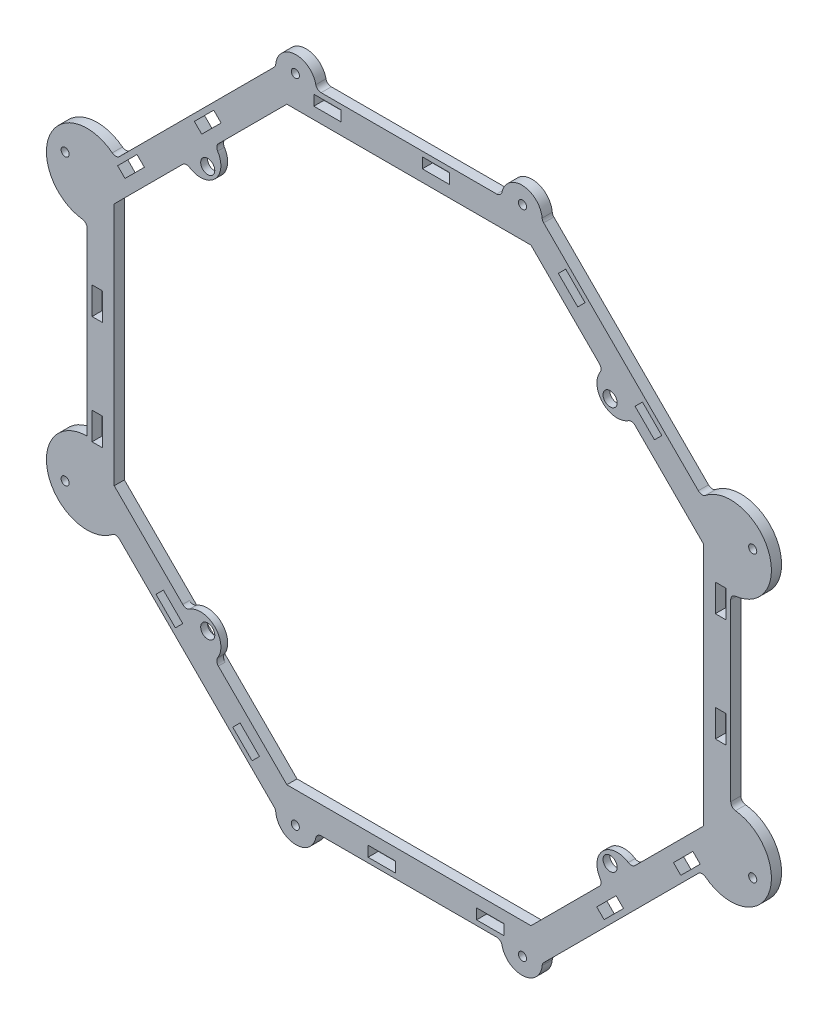
SolidWorks part; units mm, degrees
material "6061-T6 (SS)"
ref_plane "Front Plane" through (0, 0, 0) normal (0, 0, 1) x (1, 0, 0)
ref_plane "Top Plane" through (0, 0, 0) normal (0, 1, 0) x (1, 0, 0)
ref_plane "Right Plane" through (0, 0, 0) normal (1, 0, 0) x (0, 0, -1)
sketch "Sketch1" plane through (0, 0, 0) normal (0, 0, 1) x (1, 0, 0)
  line L0 (-150.6696, -62.417) -> (-62.404, -150.675)
  line L1 (-137.9698, -57.1559) -> (-57.1441, -137.9748)
  line L2 (-57.1441, -137.9748) -> (57.1559, -137.9698)
  line L3 (57.1559, -137.9698) -> (137.9748, -57.1441)
  line L4 (137.9748, -57.1441) -> (137.9698, 57.1559)
  line L5 (137.9698, 57.1559) -> (57.1441, 137.9748)
  line L6 (57.1441, 137.9748) -> (-57.1559, 137.9698)
  line L7 (-57.1559, 137.9698) -> (-137.9748, 57.1441)
  line L8 (-137.9748, 57.1441) -> (-137.9698, -57.1559)
  line L9 (-62.404, -150.675) -> (62.417, -150.6696)
  line L10 (62.417, -150.6696) -> (150.675, -62.404)
  line L11 (150.675, -62.404) -> (150.6696, 62.417)
  line L12 (150.6696, 62.417) -> (62.404, 150.675)
  line L13 (62.404, 150.675) -> (-62.417, 150.6696)
  line L14 (-62.417, 150.6696) -> (-150.675, 62.404)
  line L15 (-150.675, 62.404) -> (-150.6696, -62.417)
  circle A0 centre (0, 0) radius 137.9723 construction
  circle A1 centre (0, 0) radius 150.6723 construction
  dimension "D2" = 12.7
  dimension "D1" = 114.3
extrude "Boss-Extrude1" add sketch "Sketch1" along normal blind 4.7625
sketch "Sketch2" plane through (0, 0, 4.7625) normal (0, 0, 1) x (1, 0, 0)
  line L0 (57.1441, 137.9748) -> (-57.1559, 137.9698) construction
  line L1 (-57.1559, 137.9698) -> (-137.9748, 57.1441) construction
  line L2 (-104.3003, 90.8215) -> (-90.8305, 104.2924)
  line L3 (106.5368, 106.546) -> (97.5569, 97.5654) construction
  line L4 (-0.0059, 137.9723) -> (0.0059, -137.9723) construction
  line L5 (-57.1441, -137.9748) -> (57.1559, -137.9698) construction
  line L6 (-150.6723, -0.0065) -> (150.6723, 0.0065) construction
  line L7 (-150.675, 62.404) -> (-150.6696, -62.417) construction
  line L8 (150.675, -62.404) -> (150.6696, 62.417) construction
  line L9 (-106.546, 106.5368) -> (-97.5654, 97.5569) construction
  line L10 (-62.417, 150.6696) -> (-150.675, 62.404) construction
  line L11 (104.2924, 90.8305) -> (90.8215, 104.3003)
  line L12 (-106.5368, -106.546) -> (-97.5569, -97.5654) construction
  line L13 (106.546, -106.5368) -> (97.5654, -97.5569) construction
  line L14 (104.3003, -90.8215) -> (90.8305, -104.2924)
  line L15 (-104.2924, -90.8305) -> (-90.8215, -104.3003)
  line L16 (-97.5654, 97.5569) -> (-90.8299, 90.822) construction
  line L17 (97.5569, 97.5654) -> (90.822, 90.8299) construction
  line L18 (-97.5569, -97.5654) -> (-90.822, -90.8299) construction
  line L19 (97.5654, -97.5569) -> (90.8299, -90.822) construction
  arc A0 (-90.8305, 104.2924) -> (-104.3003, 90.8215) centre (-97.5654, 97.5569) cw
  arc A1 (90.8215, 104.3003) -> (104.2924, 90.8305) centre (97.5569, 97.5654) ccw
  arc A2 (90.8305, -104.2924) -> (104.3003, -90.8215) centre (97.5654, -97.5569) cw
  arc A3 (-90.8215, -104.3003) -> (-104.2924, -90.8305) centre (-97.5569, -97.5654) ccw
  circle A4 centre (-94.1976, 94.1895) radius 3.302
  circle A5 centre (94.1895, 94.1976) radius 3.302
  circle A6 centre (-94.1895, -94.1976) radius 3.302
  circle A7 centre (94.1976, -94.1895) radius 3.302
  dimension "D1" = 9.525
  dimension "D2" = 6.604
extrude "Boss-Extrude2" add sketch "Sketch2" against normal blind 3.175
sketch "Sketch3" plane through (0, 0, 4.7625) normal (0, 0, 1) x (1, 0, 0)
  line L0 (-57.1559, 137.9698) -> (-57.1559, 150.6698) construction
  line L1 (62.404, 150.675) -> (-62.417, 150.6696) construction
  line L2 (57.1441, 137.9748) -> (57.1441, 150.6748) construction
  line L3 (-57.1559, 145.9073) -> (57.1441, 145.9123) construction
  line L4 (-0.0059, 137.9723) -> (0.0059, -137.9723) construction
  line L5 (-31.6924, 148.3466) -> (-44.5194, 148.3466)
  line L6 (-31.6924, 148.3466) -> (-31.6924, 143.4698)
  line L7 (-31.6924, 143.4698) -> (-44.5194, 143.4698)
  line L8 (-44.5194, 148.3466) -> (-44.5194, 143.4698)
  line L9 (-31.6924, 148.3466) -> (-44.5194, 143.4698) construction
  line L10 (-31.6924, 143.4698) -> (-44.5194, 148.3466) construction
  line L17 (19.1076, 148.3488) -> (6.2806, 148.3488)
  line L18 (19.1076, 148.3488) -> (19.1076, 143.472)
  line L19 (19.1076, 143.472) -> (6.2806, 143.472)
  line L20 (6.2806, 148.3488) -> (6.2806, 143.472)
  line L21 (19.1076, 148.3488) -> (6.2806, 143.472) construction
  line L22 (19.1076, 143.472) -> (6.2806, 148.3488) construction
  line L29 (57.1441, 137.9748) -> (-57.1559, 137.9698) construction
  line L30 (-57.1441, -137.9748) -> (57.1559, -137.9698) construction
  line L31 (-137.9723, -0.0059) -> (137.9723, 0.0059) construction
  line L32 (-137.9748, 57.1441) -> (-137.9698, -57.1559) construction
  line L33 (137.9748, -57.1441) -> (137.9698, 57.1559) construction
  line L34 (106.5368, 106.546) -> (-106.5368, -106.546) construction
  line L35 (150.6696, 62.417) -> (62.404, 150.675) construction
  line L36 (-150.6696, -62.417) -> (-62.404, -150.675) construction
  line L37 (-106.546, 106.5368) -> (106.546, -106.5368) construction
  line L38 (-62.417, 150.6696) -> (-150.675, 62.404) construction
  line L39 (62.417, -150.6696) -> (150.675, -62.404) construction
  line L112 (82.4869, 127.3068) -> (73.4169, 136.3769)
  line L113 (82.4869, 127.3068) -> (79.0385, 123.8584)
  line L114 (82.4869, 127.3068) -> (69.9684, 132.9284) construction
  line L115 (79.0385, 123.8584) -> (73.4169, 136.3769) construction
  line L116 (73.4169, 136.3769) -> (69.9684, 132.9284)
  line L117 (79.0385, 123.8584) -> (69.9684, 132.9284)
  line L118 (114.9611, 87.9389) -> (105.891, 97.009)
  line L119 (118.4095, 91.3873) -> (114.9611, 87.9389)
  line L120 (118.4095, 91.3873) -> (109.3394, 100.4574)
  line L121 (109.3394, 100.4574) -> (105.891, 97.009)
  line L122 (118.4095, 91.3873) -> (105.891, 97.009) construction
  line L123 (114.9611, 87.9389) -> (109.3394, 100.4574) construction
  line L124 (148.3466, 31.6924) -> (148.3466, 44.5194)
  line L125 (148.3466, 31.6924) -> (143.4698, 31.6924)
  line L126 (148.3466, 31.6924) -> (143.4698, 44.5194) construction
  line L127 (143.4698, 31.6924) -> (148.3466, 44.5194) construction
  line L128 (148.3466, 44.5194) -> (143.4698, 44.5194)
  line L129 (143.4698, 31.6924) -> (143.4698, 44.5194)
  line L130 (143.472, -19.1076) -> (143.472, -6.2806)
  line L131 (148.3488, -19.1076) -> (143.472, -19.1076)
  line L132 (148.3488, -19.1076) -> (148.3488, -6.2806)
  line L133 (148.3488, -6.2806) -> (143.472, -6.2806)
  line L134 (148.3488, -19.1076) -> (143.472, -6.2806) construction
  line L135 (143.472, -19.1076) -> (148.3488, -6.2806) construction
  line L136 (127.3068, -82.4869) -> (136.3769, -73.4169)
  line L137 (127.3068, -82.4869) -> (123.8584, -79.0385)
  line L138 (127.3068, -82.4869) -> (132.9284, -69.9684) construction
  line L139 (123.8584, -79.0385) -> (136.3769, -73.4169) construction
  line L140 (136.3769, -73.4169) -> (132.9284, -69.9684)
  line L141 (123.8584, -79.0385) -> (132.9284, -69.9684)
  line L142 (87.9389, -114.9611) -> (97.009, -105.891)
  line L143 (91.3873, -118.4095) -> (87.9389, -114.9611)
  line L144 (91.3873, -118.4095) -> (100.4574, -109.3394)
  line L145 (100.4574, -109.3394) -> (97.009, -105.891)
  line L146 (91.3873, -118.4095) -> (97.009, -105.891) construction
  line L147 (87.9389, -114.9611) -> (100.4574, -109.3394) construction
  line L148 (31.6924, -148.3466) -> (44.5194, -148.3466)
  line L149 (31.6924, -148.3466) -> (31.6924, -143.4698)
  line L150 (31.6924, -148.3466) -> (44.5194, -143.4698) construction
  line L151 (31.6924, -143.4698) -> (44.5194, -148.3466) construction
  line L152 (44.5194, -148.3466) -> (44.5194, -143.4698)
  line L153 (31.6924, -143.4698) -> (44.5194, -143.4698)
  line L154 (-19.1076, -143.472) -> (-6.2806, -143.472)
  line L155 (-19.1076, -148.3488) -> (-19.1076, -143.472)
  line L156 (-19.1076, -148.3488) -> (-6.2806, -148.3488)
  line L157 (-6.2806, -148.3488) -> (-6.2806, -143.472)
  line L158 (-19.1076, -148.3488) -> (-6.2806, -143.472) construction
  line L159 (-19.1076, -143.472) -> (-6.2806, -148.3488) construction
  line L160 (-82.4869, -127.3068) -> (-73.4169, -136.3769)
  line L161 (-82.4869, -127.3068) -> (-79.0385, -123.8584)
  line L162 (-82.4869, -127.3068) -> (-69.9684, -132.9284) construction
  line L163 (-79.0385, -123.8584) -> (-73.4169, -136.3769) construction
  line L164 (-73.4169, -136.3769) -> (-69.9684, -132.9284)
  line L165 (-79.0385, -123.8584) -> (-69.9684, -132.9284)
  line L166 (-114.9611, -87.9389) -> (-105.891, -97.009)
  line L167 (-118.4095, -91.3873) -> (-114.9611, -87.9389)
  line L168 (-118.4095, -91.3873) -> (-109.3394, -100.4574)
  line L169 (-109.3394, -100.4574) -> (-105.891, -97.009)
  line L170 (-118.4095, -91.3873) -> (-105.891, -97.009) construction
  line L171 (-114.9611, -87.9389) -> (-109.3394, -100.4574) construction
  line L172 (-148.3466, -31.6924) -> (-148.3466, -44.5194)
  line L173 (-148.3466, -31.6924) -> (-143.4698, -31.6924)
  line L174 (-148.3466, -31.6924) -> (-143.4698, -44.5194) construction
  line L175 (-143.4698, -31.6924) -> (-148.3466, -44.5194) construction
  line L176 (-148.3466, -44.5194) -> (-143.4698, -44.5194)
  line L177 (-143.4698, -31.6924) -> (-143.4698, -44.5194)
  line L178 (-143.472, 19.1076) -> (-143.472, 6.2806)
  line L179 (-148.3488, 19.1076) -> (-143.472, 19.1076)
  line L180 (-148.3488, 19.1076) -> (-148.3488, 6.2806)
  line L181 (-148.3488, 6.2806) -> (-143.472, 6.2806)
  line L182 (-148.3488, 19.1076) -> (-143.472, 6.2806) construction
  line L183 (-143.472, 19.1076) -> (-148.3488, 6.2806) construction
  line L184 (-127.3068, 82.4869) -> (-136.3769, 73.4169)
  line L185 (-127.3068, 82.4869) -> (-123.8584, 79.0385)
  line L186 (-127.3068, 82.4869) -> (-132.9284, 69.9684) construction
  line L187 (-123.8584, 79.0385) -> (-136.3769, 73.4169) construction
  line L188 (-136.3769, 73.4169) -> (-132.9284, 69.9684)
  line L189 (-123.8584, 79.0385) -> (-132.9284, 69.9684)
  line L190 (-87.9389, 114.9611) -> (-97.009, 105.891)
  line L191 (-91.3873, 118.4095) -> (-87.9389, 114.9611)
  line L192 (-91.3873, 118.4095) -> (-100.4574, 109.3394)
  line L193 (-100.4574, 109.3394) -> (-97.009, 105.891)
  line L194 (-91.3873, 118.4095) -> (-97.009, 105.891) construction
  line L195 (-87.9389, 114.9611) -> (-100.4574, 109.3394) construction
  point P10 (-38.1059, 145.9082)
  point P20 (12.6941, 145.9104)
  dimension "D1" = 4.8768
  dimension "D2" = 12.827
  dimension "D3" = 19.05
  dimension "D4" = 50.8
  dimension "D5" = 7.9375
  dimension "D6" = 7.9375
  dimension "D7" = 4.8768
  dimension "D8" = 8
  dimension "D9" = 12.827
extrude "Panel Slots" cut sketch "Sketch3" against normal through all
sketch "Sketch4" plane through (0, 0, 4.7625) normal (0, 0, 1) x (1, 0, 0)
  line L0 (-137.9748, 57.1441) -> (-137.9698, -57.1559) construction
  circle A0 centre (0, 0) radius 137.9723 construction
sketch "Sketch5" [suppressed] plane through (0, 0, 3.175) normal (0, 0, 1) x (1, 0, 0)
  line L0 (57.1441, 137.9748) -> (-57.1559, 137.9698) construction
  line L1 (-57.1559, 137.9698) -> (-90.8305, 104.2924) construction
  line L2 (-75.1157, 120.0086) -> (-57.1559, 137.9698)
  line L3 (-57.1559, 137.9698) -> (-31.7559, 137.9709)
  line L4 (-0.0065, 150.6723) -> (0.0065, -150.6723) construction
  line L5 (62.404, 150.675) -> (-62.417, 150.6696) construction
  line L6 (-62.404, -150.675) -> (62.417, -150.6696) construction
  line L7 (-150.6723, -0.0065) -> (150.6723, 0.0065) construction
  line L8 (-150.675, 62.404) -> (-150.6696, -62.417) construction
  line L9 (150.675, -62.404) -> (150.6696, 62.417) construction
  line L10 (75.1053, 120.015) -> (57.1441, 137.9748)
  line L11 (57.1441, 137.9748) -> (31.7441, 137.9737)
  line L12 (57.1559, -137.9698) -> (31.7559, -137.9709)
  line L13 (75.1157, -120.0086) -> (57.1559, -137.9698)
  line L14 (-75.1053, -120.015) -> (-57.1441, -137.9748)
  line L15 (-57.1441, -137.9748) -> (-31.7441, -137.9737)
  line L16 (137.9698, 57.1559) -> (104.2924, 90.8305) construction
  line L17 (137.9748, -57.1441) -> (137.9698, 57.1559) construction
  line L18 (104.3003, -90.8215) -> (137.9748, -57.1441) construction
  line L19 (137.9704, 44.4559) -> (137.9698, 57.1559)
  line L20 (137.9698, 57.1559) -> (128.9892, 66.1358)
  line L21 (128.9949, -66.1247) -> (137.9748, -57.1441)
  line L22 (137.9748, -57.1441) -> (137.9742, -44.4441)
  line L23 (-137.9698, -57.1559) -> (-137.9704, -44.4559)
  line L24 (-128.9892, -66.1358) -> (-137.9698, -57.1559)
  line L25 (-137.9742, 44.4441) -> (-137.9748, 57.1441)
  line L26 (-137.9748, 57.1441) -> (-128.9949, 66.1247)
  arc A0 (-31.7559, 137.9709) -> (-75.1157, 120.0086) centre (-57.1559, 137.9698) cw
  arc A1 (31.7441, 137.9737) -> (75.1053, 120.015) centre (57.1441, 137.9748) ccw
  arc A2 (31.7559, -137.9709) -> (75.1157, -120.0086) centre (57.1559, -137.9698) cw
  arc A3 (-31.7441, -137.9737) -> (-75.1053, -120.015) centre (-57.1441, -137.9748) ccw
  arc A4 (128.9892, 66.1358) -> (137.9704, 44.4559) centre (137.9698, 57.1559) ccw
  arc A5 (137.9742, -44.4441) -> (128.9949, -66.1247) centre (137.9748, -57.1441) ccw
  arc A6 (-137.9704, -44.4559) -> (-128.9892, -66.1358) centre (-137.9698, -57.1559) cw
  arc A7 (-128.9949, 66.1247) -> (-137.9742, 44.4441) centre (-137.9748, 57.1441) cw
  dimension "D1" = 25.4
  dimension "D2" = 12.7
  dimension "D3" = 12.7
extrude "Boss-Extrude3" [suppressed] add sketch "Sketch5" against normal blind 3.175
sketch "Sketch8" plane through (0, 0, 4.7625) normal (0, 0, 1) x (1, 0, 0)
  line L0 (-57.1559, 137.9698) -> (-90.8305, 104.2924) construction
  line L1 (-79.6056, 115.5182) -> (-70.6257, 124.4989)
  line L2 (-0.0065, 150.6723) -> (0.0065, -150.6723) construction
  line L3 (62.404, 150.675) -> (-62.417, 150.6696) construction
  line L4 (-62.404, -150.675) -> (62.417, -150.6696) construction
  line L5 (-150.6723, -0.0065) -> (150.6723, 0.0065) construction
  line L6 (-150.675, 62.404) -> (-150.6696, -62.417) construction
  line L7 (150.675, -62.404) -> (150.6696, 62.417) construction
  line L8 (79.5957, 115.5251) -> (70.615, 124.505)
  line L9 (79.6056, -115.5182) -> (70.6257, -124.4989)
  line L10 (-79.5957, -115.5251) -> (-70.615, -124.505)
  line L11 (-57.1559, 137.9698) -> (-90.8305, 104.2924) construction
  arc A0 (-70.6257, 124.4989) -> (-79.6056, 115.5182) centre (-75.1157, 120.0086) cw
  arc A1 (70.615, 124.505) -> (79.5957, 115.5251) centre (75.1053, 120.015) ccw
  arc A2 (70.6257, -124.4989) -> (79.6056, -115.5182) centre (75.1157, -120.0086) cw
  arc A3 (-70.615, -124.505) -> (-79.5957, -115.5251) centre (-75.1053, -120.015) ccw
  dimension "D1" = 6.35
  dimension "D2" = 12.7
  dimension "D3" = 19.05
extrude "Boss-Extrude4" [suppressed] add sketch "Sketch8" against normal blind 4.7625
hole_wizard "#6 Clearance Hole1" [suppressed] positions "Sketch7" profile "Sketch6" hole size "#6" standard "Ansi Inch"
sketch "Sketch7" plane through (0, 0, 4.7625) normal (0, 0, 1) x (1, 0, 0)
  line L11 (0, 137.9723) -> (0, -137.9723) construction
  line L16 (73.025, 117.475) -> (-73.025, 117.475)
  line L17 (73.025, 117.475) -> (73.025, -117.475)
  line L18 (73.025, -117.475) -> (-73.025, -117.475)
  line L19 (-73.025, 117.475) -> (-73.025, -117.475)
  line L20 (73.025, 117.475) -> (-73.025, -117.475) construction
  line L21 (73.025, -117.475) -> (-73.025, 117.475) construction
  circle A6 centre (0, 0) radius 137.9723 construction
  point P56 (73.025, 117.475)
  point P58 (73.025, -117.475)
  point P70 (-73.025, 117.475)
  point P73 (-73.025, -117.475)
  point P75 (0, 0)
  dimension "D1" = 234.95
  dimension "D2" = 146.05
sketch "Sketch6" plane through (73.025, 117.475, 4.7625) normal (1, 0, 0) x (0, -1, 0)
  line L0 (0, 0) -> (0, 26.5408)
  line L1 (0, 26.5408) -> (1.8986, 25.4)
  line L2 (1.8986, 25.4) -> (1.8986, 0)
  line L5 (1.8986, 0) -> (0, 0)
  line L10 (0, 26.5408) -> (-1.8986, 25.4) construction
  line L11 (0, -6.35) -> (0, 107.95) construction
  dimension "Hole Dia." = 3.7973
  dimension "Hole Depth" = 25.4
  dimension "Drill Angle" = 118
sketch "Sketch9" plane through (0, 0, 4.7625) normal (0, 0, 1) x (1, 0, 0)
  line L0 (62.404, 150.675) -> (-62.417, 150.6696) construction
  line L1 (-62.417, 150.6696) -> (-43.367, 150.6704)
  line L2 (-0.0065, 150.6723) -> (0.0065, -150.6723) construction
  line L3 (-62.404, -150.675) -> (62.417, -150.6696) construction
  line L4 (150.6723, 0.0065) -> (-150.6723, -0.0065) construction
  line L5 (150.675, -62.404) -> (150.6696, 62.417) construction
  line L6 (-150.675, 62.404) -> (-150.6696, -62.417) construction
  line L7 (62.404, 150.675) -> (43.354, 150.6742)
  line L8 (62.417, -150.6696) -> (43.367, -150.6704)
  line L9 (-62.404, -150.675) -> (-43.354, -150.6742)
  arc A0 (-62.417, 150.6696) -> (-43.367, 150.6704) centre (-52.892, 150.67) cw
  arc A1 (62.404, 150.675) -> (43.354, 150.6742) centre (52.879, 150.6746) ccw
  arc A2 (62.417, -150.6696) -> (43.367, -150.6704) centre (52.892, -150.67) cw
  arc A3 (-62.404, -150.675) -> (-43.354, -150.6742) centre (-52.879, -150.6746) ccw
  dimension "D2" = 9.525
  dimension "D1" = 19.05
extrude "Boss-Extrude8" add sketch "Sketch9" against normal blind 4.7625
hole_wizard "#6 Clearance Hole2" positions "Sketch12" profile "Sketch11" hole size "#6" standard "Ansi Inch"
sketch "Sketch12" plane through (0, 0, 4.7625) normal (0, 0, 1) x (1, 0, 0)
  line L1 (53.1812, 152.4) -> (-53.1813, 152.4)
  line L2 (53.1812, 152.4) -> (53.1812, -152.4)
  line L3 (53.1812, -152.4) -> (-53.1812, -152.4)
  line L4 (-53.1813, 152.4) -> (-53.1812, -152.4)
  line L5 (53.1812, 152.4) -> (-53.1812, -152.4) construction
  line L6 (53.1812, -152.4) -> (-53.1813, 152.4) construction
  point P0 (-53.1813, 152.4)
  point P1 (53.1812, 152.4)
  point P3 (53.1812, -152.4)
  point P5 (-53.1812, -152.4)
  point P8 (0, 0)
  dimension "D1" = 304.8
  dimension "D2" = 106.3625
sketch "Sketch11" plane through (-53.1813, 152.4, 4.7625) normal (1, 0, 0) x (0, -1, 0)
  line L0 (0, 0) -> (0, 26.5408)
  line L1 (0, 26.5408) -> (1.8986, 25.4)
  line L2 (1.8986, 25.4) -> (1.8986, 0)
  line L5 (1.8986, 0) -> (0, 0)
  line L10 (0, 26.5408) -> (-1.8986, 25.4) construction
  line L11 (0, -6.35) -> (0, 107.95) construction
  dimension "Hole Dia." = 3.7973
  dimension "Hole Depth" = 25.4
  dimension "Drill Angle" = 118
sketch "Sketch13" plane through (0, 0, 4.7625) normal (0, 0, 1) x (1, 0, 0)
  line L0 (150.675, -62.404) -> (150.6696, 62.417) construction
  line L1 (150.6696, 62.417) -> (62.404, 150.675) construction
  line L2 (62.417, -150.6696) -> (150.675, -62.404) construction
  line L3 (137.2052, -75.875) -> (150.675, -62.404)
  line L4 (150.675, -62.404) -> (150.6742, -43.354)
  line L5 (137.1987, 75.8868) -> (150.6696, 62.417)
  line L6 (150.6696, 62.417) -> (150.6704, 43.367)
  line L7 (-0.0065, 150.6723) -> (0.0065, -150.6723) construction
  line L8 (43.354, 150.6742) -> (-43.367, 150.6704) construction
  line L9 (-43.354, -150.6742) -> (43.367, -150.6704) construction
  line L10 (-150.675, 62.404) -> (-150.6742, 43.354)
  line L11 (-137.2052, 75.875) -> (-150.675, 62.404)
  line L12 (-150.6696, -62.417) -> (-150.6704, -43.367)
  line L13 (-137.1987, -75.8868) -> (-150.6696, -62.417)
  arc A0 (150.6704, 43.367) -> (137.1987, 75.8868) centre (150.6696, 62.417) ccw
  arc A1 (150.6742, -43.354) -> (137.2052, -75.875) centre (150.675, -62.404) cw
  arc A2 (-150.6704, -43.367) -> (-137.1987, -75.8868) centre (-150.6696, -62.417) ccw
  arc A3 (-150.6742, 43.354) -> (-137.2052, 75.875) centre (-150.675, 62.404) cw
  dimension "D1" = 19.05
  dimension "D2" = 19.05
extrude "Boss-Extrude9" add sketch "Sketch13" against normal blind 4.7625
hole_wizard "#6 Clearance Hole3" positions "Sketch15" profile "Sketch14" hole size "#6" standard "Ansi Inch"
sketch "Sketch15" plane through (0, 0, 4.7625) normal (0, 0, 1) x (1, 0, 0)
  line L0 (-168.2752, 69.6934) -> (-137.9748, 57.1441) construction
  line L2 (-168.2692, -69.7079) -> (-137.9698, -57.1559) construction
  line L4 (168.2752, -69.6934) -> (137.9748, -57.1441) construction
  line L6 (168.2692, 69.7079) -> (137.9698, 57.1559) construction
  line L8 (-150.6723, -0.0065) -> (150.6723, 0.0065) construction
  line L9 (-150.6742, 43.354) -> (-150.6704, -43.367) construction
  line L10 (150.6742, -43.354) -> (150.6704, 43.367) construction
  arc A0 (-137.2052, 75.875) -> (-150.6742, 43.354) centre (-150.675, 62.404) ccw construction
  arc A1 (-150.6704, -43.367) -> (-137.1987, -75.8868) centre (-150.6696, -62.417) ccw construction
  arc A2 (137.2052, -75.875) -> (150.6742, -43.354) centre (150.675, -62.404) ccw construction
  arc A3 (150.6704, 43.367) -> (137.1987, 75.8868) centre (150.6696, 62.417) ccw construction
  point P0 (160.9637, 66.6815)
  point P1 (160.9716, -66.6685)
  point P3 (-160.9637, -66.6815)
  point P5 (-160.9716, 66.6685)
  dimension "D1" = 66.675
  dimension "D2" = 66.675
  dimension "D3" = 66.675
  dimension "D4" = 66.675
sketch "Sketch14" plane through (160.9637, 66.6815, 4.7625) normal (1, 0, 0) x (0, -1, 0)
  line L0 (0, 0) -> (0, 26.5408)
  line L1 (0, 26.5408) -> (1.8986, 25.4)
  line L2 (1.8986, 25.4) -> (1.8986, 0)
  line L5 (1.8986, 0) -> (0, 0)
  line L10 (0, 26.5408) -> (-1.8987, 25.4) construction
  line L11 (0, -6.35) -> (0, 107.95) construction
  dimension "Hole Dia." = 3.7973
  dimension "Hole Depth" = 25.4
  dimension "Drill Angle" = 118
fillet "Fillet1" radius 2.54 15 edges at (-137.1987, -75.8868, 2.3813) (-62.404, -150.675, 2.3813) (-43.354, -150.6742, 2.3813) (62.417, -150.6696, 2.3813) (43.367, -150.6704, 2.3813) (137.2052, -75.875, 2.3813) (150.6742, -43.354, 2.3813) (150.6704, 43.367, 2.3813) (137.1987, 75.8868, 2.3813) (62.404, 150.675, 2.3813) (43.354, 150.6742, 2.3813) (-43.367, 150.6704, 2.3813) (-62.417, 150.6696, 2.3813) (-137.2052, 75.875, 2.3813) (-150.6742, 43.354, 2.3813)
fillet "Fillet2" radius 2.54 8 edges at (-90.8215, -104.3003, 3.175) (-104.2924, -90.8305, 3.175) (104.3003, -90.8215, 3.175) (90.8305, -104.2924, 3.175) (90.8215, 104.3003, 3.175) (104.2924, 90.8305, 3.175) (-104.3003, 90.8215, 3.175) (-90.8305, 104.2924, 3.175)
